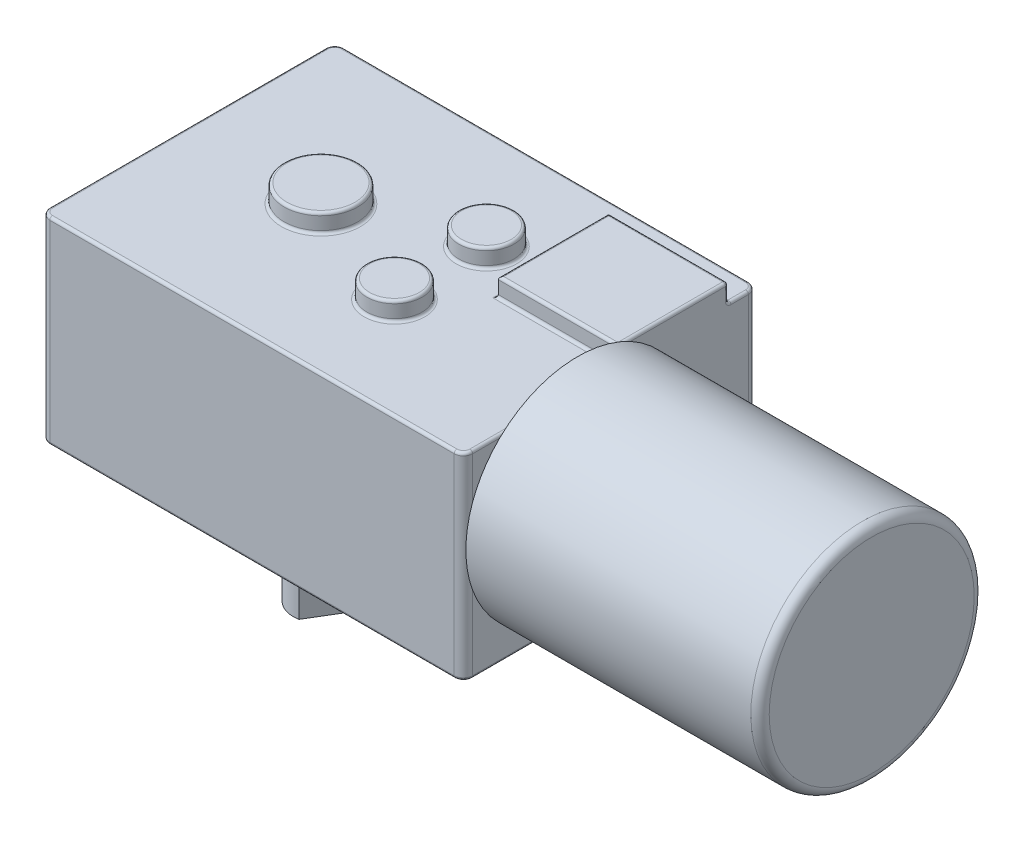
SolidWorks part; units mm, degrees
ref_plane "Front Plane" through (0, 0, 0) normal (0, 0, 1) x (1, 0, 0)
ref_plane "Top Plane" through (0, 0, 0) normal (0, 1, 0) x (1, 0, 0)
ref_plane "Right Plane" through (0, 0, 0) normal (1, 0, 0) x (0, 0, -1)
sketch "Sketch1" plane through (0, 0, 0) normal (0, 1, 0) x (1, 0, 0)
  line L1 (-23, 16) -> (23, 16)
  line L2 (-23, 16) -> (-23, -16)
  line L3 (-23, -16) -> (23, -16)
  line L4 (23, 16) -> (23, -16)
  line L5 (-23, 16) -> (23, -16) construction
  line L6 (-23, -16) -> (23, 16) construction
  point P0 (0, 0)
  dimension "D1" = 32
  dimension "D2" = 46
extrude "Boss-Extrude1" add sketch "Sketch1" along normal blind 21.5
fillet "Fillet1" radius 1 4 edges at (-23, 10.75, -16) (-23, 10.75, 16) (23, 10.75, -16) (23, 10.75, 16)
sketch "Sketch2" plane through (0, 21.5, 0) normal (0, 1, 0) x (1, 0, 0)
  line L0 (23, -15) -> (23, 15) construction
  line L1 (23, 12.8) -> (10, 12.8)
  line L2 (23, 12.8) -> (23, 0.8)
  line L3 (23, 0.8) -> (10, 0.8)
  line L4 (10, 12.8) -> (10, 0.8)
  line L5 (22, 16) -> (-22, 16) construction
  dimension "D1" = 3.2
  dimension "D2" = 12
  dimension "D3" = 13
extrude "Boss-Extrude2" add sketch "Sketch2" along normal blind 2
sketch "Sketch3" plane through (0, 21.5, 0) normal (0, 1, 0) x (1, 0, 0)
  line L0 (-23, 0) -> (-8.5, 0) construction
  line L1 (-23, 15) -> (-23, -15) construction
  line L3 (-8.5, 0) -> (4.5, 0) construction
  line L4 (4.5, 0) -> (4.5, 5) construction
  line L5 (4.5, 0) -> (4.5, -5) construction
  circle A0 centre (-8.5, 0) radius 4
  circle A1 centre (4.5, 5) radius 3
  circle A2 centre (4.5, -5) radius 3
  dimension "D2" = 8
  dimension "D3" = 6
  dimension "D4" = 6
  dimension "D1" = 14.5
  dimension "D5" = 13
  dimension "D6" = 5
  dimension "D7" = 5
extrude "Boss-Extrude3" add sketch "Sketch3" along normal blind 2
sketch "Sketch4" plane through (0, 0, 0) normal (0, -1, 0) x (1, 0, 0)
  line L0 (-23, 0) -> (-8.5, 0) construction
  line L1 (-23, -15) -> (-23, 15) construction
  line L2 (-16.4, 9.4) -> (16.4, 9.4) construction
  line L3 (16.4, 9.4) -> (16.4, -9.4) construction
  line L4 (16.4, -9.4) -> (-16.4, -9.4) construction
  line L5 (-16.4, -9.4) -> (-16.4, 9.4) construction
  line L6 (-22, 16) -> (22, 16) construction
  line L7 (23, 15) -> (23, -15) construction
  line L8 (22, -16) -> (-22, -16) construction
  circle A0 centre (-8.5, 0) radius 6.75
  circle A1 centre (-16.4, 9.4) radius 4
  circle A2 centre (-16.4, 9.4) radius 1.5
  circle A3 centre (-16.4, -9.4) radius 4
  circle A4 centre (-16.4, -9.4) radius 1.5
  circle A6 centre (16.4, -9.4) radius 1.5
  circle A7 centre (16.4, -9.4) radius 4
  circle A8 centre (16.4, 9.4) radius 1.5
  circle A9 centre (16.4, 9.4) radius 4
  circle A10 centre (4.5, 5) radius 3
  circle A11 centre (4.5, -5) radius 3
  dimension "D2" = 13.5
  dimension "D7" = 3
  dimension "D8" = 8
  dimension "D9" = 8
  dimension "D10" = 3
  dimension "D11" = 3
  dimension "D12" = 8
  dimension "D13" = 3
  dimension "D14" = 8
  dimension "D1" = 14.5
  dimension "D3" = 6.6
  dimension "D4" = 6.6
  dimension "D5" = 6.6
  dimension "D6" = 6.6
  dimension "D15" = 32.8
  dimension "D16" = 18.8
extrude "Boss-Extrude4" add sketch "Sketch4" along normal blind 2
fillet "Fillet2" radius 0.3 49 edges at (23, 22.5, -0.8) (23, 22.5, -12.8) (4.5, 23.5, 8) (16.5, 23.5, -0.8) (10, 23.5, -6.8) (16.5, 23.5, -12.8) (23, 23.5, -6.8) (4.5, 23.5, -2) (-8.5, 23.5, 4) (-16.4, -2, -10.9) (-16.4, -2, -13.4) (16.4, -2, -10.9) (16.4, -2, -13.4) (16.4, -2, 7.9) (16.4, -2, 5.4) (4.5, -2, -8) (4.5, -2, 2) (-16.4, -2, 7.9) (-16.4, -2, 5.4) (-22.7071, 0, 15.7071) (0, 0, 16) (22.7071, 0, 15.7071) (23, 0, 0) (22.7071, 0, -15.7071) (0, 0, -16) (-22.7071, 0, -15.7071) (-23, 0, 0) (-8.5, 0, -6.75) (-16.4, 0, 13.4) (-16.4, 0, -5.4) (16.4, 0, -5.4) (16.4, 0, 13.4) (4.5, 0, 8) (4.5, 0, -2) (23, 21.5, 7.1) (22.7071, 21.5, 15.7071) (0, 21.5, 16) (-22.7071, 21.5, 15.7071) (-23, 21.5, 0) (-22.7071, 21.5, -15.7071) (0, 21.5, -16) (22.7071, 21.5, -15.7071) (23, 21.5, -13.9) (16.5, 21.5, -12.8) (10, 21.5, -6.8) (16.5, 21.5, -0.8) (-8.5, 21.5, 4) (4.5, 21.5, -2) (4.5, 21.5, 8)
sketch "Sketch5" plane through (23, 0, 0) normal (1, 0, 0) x (0, 0, -1)
  line L0 (-3.584, 12.5) -> (0, 12.5) construction
  line L1 (0, 12.5) -> (0, 0) construction
  circle A0 centre (-3.584, 12.5) radius 12.15
  dimension "D1" = 24.3
  dimension "D2" = 12.5
extrude "Boss-Extrude5" add sketch "Sketch5" along normal blind 32
fillet "Fillet3" radius 1 1 edges at (55, 12.5, -8.566)
sketch "Sketch6" plane through (0, -2, 0) normal (0, 1, 0) x (1, 0, 0)
  circle A0 centre (-8.5, 0) radius 5
  dimension "D1" = 10
extrude "Cut-Extrude1" cut sketch "Sketch6" along normal blind 0.1
sketch "Sketch7" plane through (0, -1.9, 0) normal (0, -1, 0) x (1, 0, 0)
  circle A1 centre (-8.5, 0) radius 3
extrude "Boss-Extrude6" add sketch "Sketch7" along normal blind 14
sketch "Sketch8" plane through (0, -15.9, 0) normal (0, -1, 0) x (1, 0, 0)
  line L0 (-7.9392, 2.9471) -> (-5.6334, -0.8848)
  line L1 (-7.9392, 2.9471) -> (-4.6301, 4.9384)
  line L2 (-5.6334, -0.8848) -> (-2.3243, 1.1065)
  line L3 (-4.6301, 4.9384) -> (-2.3243, 1.1065)
  circle A0 centre (-8.5, 0) radius 3 construction
  circle A1 centre (-8.5, 0) radius 3 construction
  dimension "D1" = 2
extrude "Cut-Extrude2" cut sketch "Sketch8" against normal blind 11
